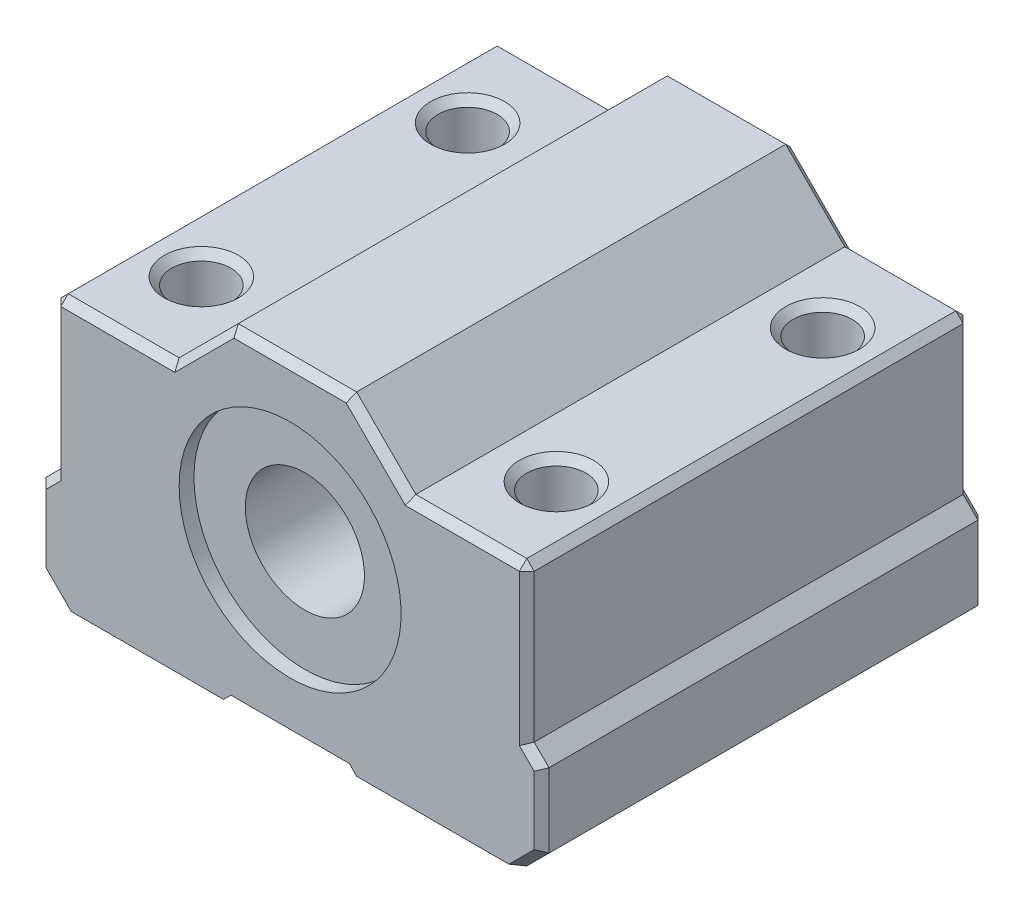
SolidWorks part; units mm, degrees
ref_plane "Plano frontal" through (0, 0, 0) normal (0, 0, 1) x (1, 0, 0)
ref_plane "Plano superior" through (0, 0, 0) normal (0, 1, 0) x (1, 0, 0)
ref_plane "Plano direito" through (0, 0, 0) normal (1, 0, 0) x (0, 0, -1)
ref_plane "Plano1" through (0, 13.3186, 0) normal (0, 1, 0) x (1, 0, 0)
sketch "Esboço1" plane through (0, 13.3186, 0) normal (0, 1, 0) x (1, 0, 0)
  line L0 (-16.9064, -30) -> (17.0936, -30)
  line L1 (17.0936, -30) -> (17.0936, 0)
  line L2 (17.0936, 0) -> (-16.9064, 0)
  line L3 (-16.9064, 0) -> (-16.9064, -30)
extrude "Ressalto-extrusão1" add sketch "Esboço1" against normal blind 22
sketch "Esboço2" plane through (0, 0, 0) normal (0, 0, -1) x (-1, 0, 0)
  line L0 (-17.0936, -2.1814) -> (-16.0936, -1.1814)
  line L1 (-16.0936, -1.1814) -> (-16.0936, 13.3186)
  line L2 (-16.0936, 13.3186) -> (-17.0936, 13.3186)
  line L3 (-17.0936, 13.3186) -> (-17.0936, -2.1814)
extrude "Corte-extrusão1" cut sketch "Esboço2" against normal through all
sketch "Esboço3" plane through (0, 0, 0) normal (0, 0, -1) x (-1, 0, 0)
  line L0 (-16.0936, 13.3186) -> (-16.0936, 9.3186)
  line L1 (-16.0936, 9.3186) -> (-8.0936, 9.3186)
  line L2 (-8.0936, 9.3186) -> (-4.0936, 13.3186)
  line L3 (-4.0936, 13.3186) -> (-16.0936, 13.3186)
extrude "Corte-extrusão2" cut sketch "Esboço3" against normal through all
sketch "Esboço4" plane through (0, 0, 0) normal (0, 0, -1) x (-1, 0, 0)
  line L0 (16.9064, 13.3186) -> (3.9064, 13.3186)
  line L1 (3.9064, 13.3186) -> (7.9064, 9.3186)
  line L2 (7.9064, 9.3186) -> (16.9064, 9.3186)
  line L3 (16.9064, 9.3186) -> (16.9064, 13.3186)
extrude "Corte-extrusão3" cut sketch "Esboço4" against normal through all
sketch "Esboço5" plane through (0, 0, 0) normal (0, 0, -1) x (-1, 0, 0)
  line L0 (15.9064, 9.3186) -> (15.9064, -1.1814)
  line L1 (15.9064, -1.1814) -> (16.9064, -2.1814)
  line L2 (16.9064, -2.1814) -> (16.9064, 9.3186)
  line L3 (16.9064, 9.3186) -> (15.9064, 9.3186)
extrude "Corte-extrusão4" cut sketch "Esboço5" against normal through all
sketch "Esboço6" plane through (0, 0, 0) normal (0, 0, -1) x (-1, 0, 0)
  line L0 (-4.5936, -8.6814) -> (4.4064, -8.6814)
  line L1 (4.4064, -8.6814) -> (3.9064, -8.1814)
  line L2 (3.9064, -8.1814) -> (-4.0936, -8.1814)
  line L3 (-4.0936, -8.1814) -> (-4.5936, -8.6814)
extrude "Corte-extrusão5" cut sketch "Esboço6" against normal through all
ref_plane "Plano2" through (0, 2.3186, 0) normal (0, -1, 0) x (1, 0, 0)
sketch "Esboço7" plane through (0, 2.3186, 0) normal (0, -1, 0) x (1, 0, 0)
  line L0 (7.5936, 30) -> (0.0936, 30)
  line L1 (0.0936, 30) -> (0.0936, 0)
  line L2 (0.0936, 0) -> (7.5936, 0)
  line L3 (7.5936, 0) -> (7.5936, 1)
  line L4 (7.5936, 1) -> (4.1186, 1)
  line L5 (4.1186, 1) -> (4.1186, 29)
  line L6 (4.1186, 29) -> (7.5936, 29)
  line L7 (7.5936, 29) -> (7.5936, 30)
  line L8 (0.0936, 30) -> (0.0936, 0) construction
revolve "Corte-Revolução1" cut sketch "Esboço7" angle 360 about L8
hole_wizard "Furo de diâmetro Ø4.0 (4)1" positions "Esboço9" profile "Esboço8" hole size "Ø4.0" standard "Ansi Metric"
sketch "Esboço9" plane through (0, 9.3186, 0) normal (0, 1, 0) x (1, 0, 0)
  point P0 (12.0936, -24)
sketch "Esboço8" plane through (12.0936, 9.3186, 24) normal (1, 0, 0) x (0, 0, 1)
  line L0 (0, 0) -> (0, 18)
  line L1 (0, 18) -> (2, 18)
  line L2 (2, 18) -> (2, 0)
  line L5 (2, 0) -> (0, 0)
  line L11 (0, -6.35) -> (0, 107.95) construction
  dimension "Thru Hole Dia." = 4
  dimension "Thru Hole Depth" = 18
hole_wizard "Furo de diâmetro Ø4.0 (4)2" positions "Esboço11" profile "Esboço10" hole size "Ø4.0" standard "Ansi Metric"
sketch "Esboço11" plane through (0, -8.6814, 0) normal (0, -1, 0) x (-1, 0, 0)
  point P0 (11.9064, -6)
  point P1 (11.9064, -24)
  point P2 (-12.0936, -6)
sketch "Esboço10" plane through (-11.9064, -8.6814, 6) normal (1, 0, 0) x (0, 0, -1)
  line L0 (0, 0) -> (0, 22)
  line L1 (0, 22) -> (2, 22)
  line L2 (2, 22) -> (2, 0)
  line L5 (2, 0) -> (0, 0)
  line L11 (0, -6.35) -> (0, 107.95) construction
  dimension "Thru Hole Dia." = 4
  dimension "Thru Hole Depth" = 22
chamfer "Chanfro1" distance 1.5 angle 45 2 edges at (17.0936, -8.6814, 15) (-16.9064, -8.6814, 15)
chamfer "Chanfro2" distance 0.5 angle 45 36 edges at (-16.1564, -7.9314, 0) (-16.9064, -4.6814, 0) (-16.4064, -1.6814, 0) (-15.9064, 4.0686, 0) (-15.9064, 9.3186, 15) (-16.1564, -7.9314, 30) (-16.9064, -4.6814, 30) (-16.4064, -1.6814, 30) (-15.9064, 4.0686, 30) (16.3436, -7.9314, 0) (17.0936, -4.6814, 0) (16.5936, -1.6814, 0) (16.0936, 4.0686, 0) (-11.9064, 9.3186, 0) (-5.9064, 11.3186, 0) (0.0936, 13.3186, 0) (6.0936, 11.3186, 0) (12.0936, 9.3186, 0) (-11.9064, 9.3186, 30) (-5.9064, 11.3186, 30) (0.0936, 13.3186, 30) (6.0936, 11.3186, 30) (12.0936, 9.3186, 30) (16.0936, 9.3186, 15) (16.0936, 4.0686, 30) (16.3436, -7.9314, 30) (16.5936, -1.6814, 30) (17.0936, -4.6814, 30) (12.0936, 9.3186, 4) (-11.9064, 9.3186, 4) (-11.9064, 9.3186, 22) (-11.9064, -8.6814, 4) (-11.9064, -8.6814, 22) (12.0936, -8.6814, 26) (12.0936, -8.6814, 4) (12.0936, 9.3186, 26)
